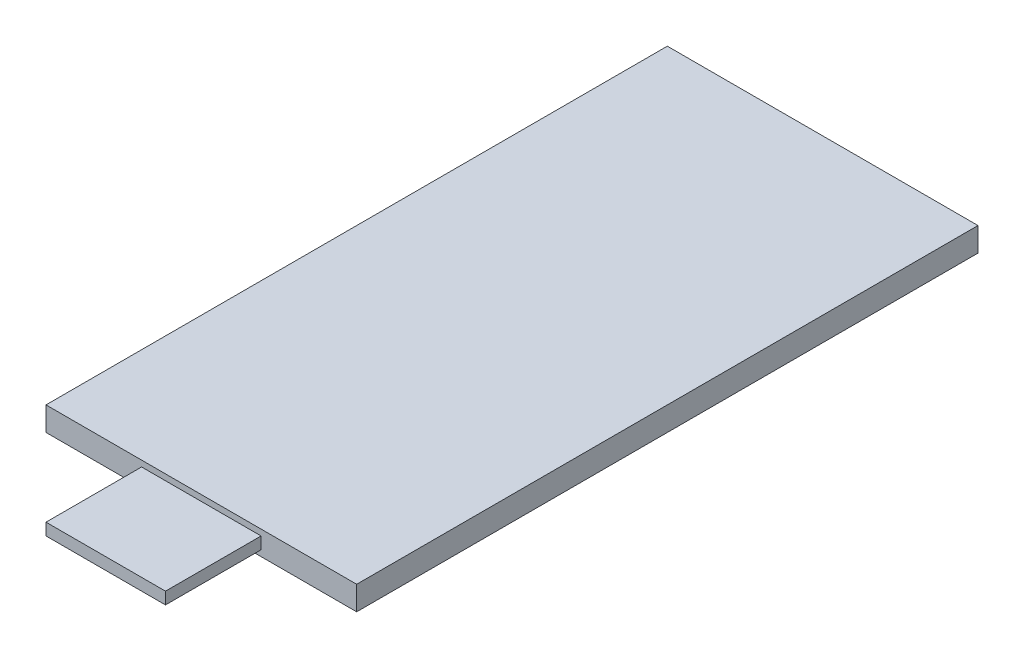
SolidWorks part; units mm, degrees
ref_plane "Front Plane" through (0, 0, 0) normal (0, 0, 1) x (1, 0, 0)
ref_plane "Top Plane" through (0, 0, 0) normal (0, 1, 0) x (1, 0, 0)
ref_plane "Right Plane" through (0, 0, 0) normal (1, 0, 0) x (0, 0, -1)
sketch "Sketch1" plane through (0, 0, 0) normal (0, 1, 0) x (1, 0, 0)
  line L1 (-13, 30) -> (13, 30)
  line L2 (-13, 30) -> (-13, -30)
  line L3 (-13, -30) -> (13, -30)
  line L4 (13, 30) -> (13, -30)
  line L5 (-13, 30) -> (13, -30) construction
  line L6 (-13, -30) -> (13, 30) construction
  point P0 (0, 0)
  dimension "D1" = 26
  dimension "D2" = 60
extrude "Boss-Extrude1" add sketch "Sketch1" along normal blind 2
sketch "Sketch9" plane through (0, 2, 0) normal (0, 1, 0) x (1, 0, 0)
  line L1 (-13, -30) -> (-5, -30)
  line L2 (-13, -30) -> (-13, -22)
  line L3 (-13, -22) -> (-5, -22)
  line L4 (-5, -30) -> (-5, -22)
  line L5 (13, -30) -> (5, -30)
  line L6 (13, -30) -> (13, -22)
  line L7 (13, -22) -> (5, -22)
  line L8 (5, -30) -> (5, -22)
  dimension "D1" = 8
  dimension "D2" = 8
  dimension "D3" = 8
  dimension "D4" = 8
extrude "Cut-Extrude1" cut sketch "Sketch9" against normal blind 2
sketch "Sketch10" plane through (0, 2, 0) normal (0, 1, 0) x (1, 0, 0)
  line L0 (-5, -30) -> (-5, -22) construction
  line L1 (-5, -22) -> (5, -22)
  line L2 (-5, -22) -> (-5, -30)
  line L3 (-5, -30) -> (5, -30)
  line L4 (5, -22) -> (5, -30)
  line L5 (-5, -22) -> (-13, -22) construction
  line L6 (5, -22) -> (5, -30) construction
extrude "Cut-Extrude2" cut sketch "Sketch10" against normal blind 0.5
sketch "Sketch11" plane through (0, 0, 0) normal (0, -1, 0) x (1, 0, 0)
  line L1 (-5, 30) -> (5, 30)
  line L2 (-5, 30) -> (-5, 22)
  line L3 (-5, 22) -> (5, 22)
  line L4 (5, 30) -> (5, 22)
extrude "Cut-Extrude3" cut sketch "Sketch11" against normal blind 0.5
